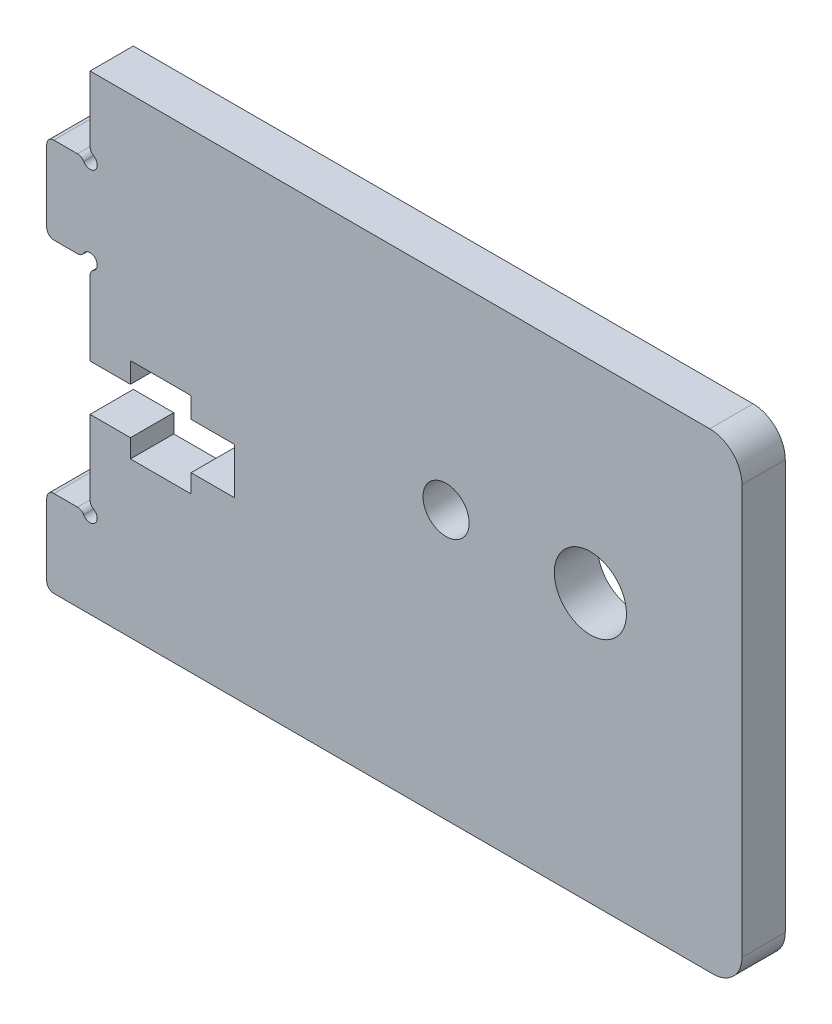
SolidWorks part; units mm, degrees
material "Plain Carbon Steel"
ref_plane "Front Plane" through (0, 0, 0) normal (0, 0, 1) x (1, 0, 0)
ref_plane "Top Plane" through (0, 0, 0) normal (0, 1, 0) x (1, 0, 0)
ref_plane "Right Plane" through (0, 0, 0) normal (1, 0, 0) x (0, 0, -1)
sketch "Sketch1" plane through (0, 0, 0) normal (0, 0, 1) x (1, 0, 0)
  line L0 (168.0271, 1038.0433) -> (213.6924, 1038.0433)
  line L1 (167.5271, 1043.5433) -> (167.5271, 1038.5433)
  line L2 (169.6611, 1044.0433) -> (168.0271, 1044.0433)
  line L3 (170.5271, 1050.0433) -> (170.5271, 1044.9093)
  line L4 (173.3271, 1050.0433) -> (170.5271, 1050.0433)
  line L5 (173.3271, 1048.7683) -> (173.3271, 1050.0433)
  line L6 (177.5271, 1048.7683) -> (173.3271, 1048.7683)
  line L7 (177.5271, 1050.0433) -> (177.5271, 1048.7683)
  line L8 (180.5271, 1050.0433) -> (177.5271, 1050.0433)
  line L9 (180.5271, 1053.2433) -> (180.5271, 1050.0433)
  line L10 (177.5271, 1053.2433) -> (180.5271, 1053.2433)
  line L11 (177.5271, 1054.6683) -> (177.5271, 1053.2433)
  line L12 (173.3271, 1054.6683) -> (177.5271, 1054.6683)
  line L13 (173.3271, 1053.2433) -> (173.3271, 1054.6683)
  line L14 (170.5271, 1053.2433) -> (173.3271, 1053.2433)
  line L15 (170.5271, 1058.3773) -> (170.5271, 1053.2433)
  line L16 (168.0271, 1059.2433) -> (169.6611, 1059.2433)
  line L17 (167.5271, 1064.7433) -> (167.5271, 1059.7433)
  line L18 (169.6611, 1065.2433) -> (168.0271, 1065.2433)
  line L19 (170.5272, 1070.6433) -> (170.5272, 1066.1093)
  line L20 (213.4564, 1070.6433) -> (170.5272, 1070.6433)
  line L21 (215.6924, 1068.4072) -> (215.6924, 1040.0433)
  arc A0 (167.5271, 1038.5433) -> (168.0271, 1038.0433) centre (168.0271, 1038.5433) ccw
  arc A1 (168.0271, 1044.0433) -> (167.5271, 1043.5433) centre (168.0271, 1043.5433) ccw
  arc A2 (170.0941, 1043.7933) -> (169.6611, 1044.0433) centre (169.6611, 1043.5433) ccw
  arc A3 (170.0941, 1043.7933) -> (170.7771, 1044.4763) centre (170.5271, 1044.0433) ccw
  arc A4 (170.5271, 1044.9093) -> (170.7771, 1044.4763) centre (171.0271, 1044.9093) ccw
  arc A5 (170.7771, 1058.8103) -> (170.5271, 1058.3773) centre (171.0271, 1058.3773) ccw
  arc A6 (170.7771, 1058.8103) -> (170.0941, 1059.4933) centre (170.5271, 1059.2433) ccw
  arc A7 (169.6611, 1059.2433) -> (170.0941, 1059.4933) centre (169.6611, 1059.7433) ccw
  arc A8 (167.5271, 1059.7433) -> (168.0271, 1059.2433) centre (168.0271, 1059.7433) ccw
  arc A9 (168.0271, 1065.2433) -> (167.5271, 1064.7433) centre (168.0271, 1064.7433) ccw
  arc A10 (170.0941, 1064.9933) -> (169.6611, 1065.2433) centre (169.6611, 1064.7433) ccw
  arc A11 (170.0941, 1064.9933) -> (170.7772, 1065.6763) centre (170.5272, 1065.2433) ccw
  arc A12 (170.5272, 1066.1093) -> (170.7772, 1065.6763) centre (171.0272, 1066.1093) ccw
  arc A13 (215.6924, 1068.4072) -> (213.4564, 1070.6433) centre (213.4564, 1068.4072) ccw
  arc A14 (213.6924, 1038.0433) -> (215.6924, 1040.0433) centre (213.6924, 1040.0433) ccw
  circle A15 centre (195.1924, 1056.6433) radius 1.6
  circle A16 centre (205.1924, 1056.6433) radius 2.5
extrude "Boss-Extrude1" add sketch "Sketch1" along normal blind 3
